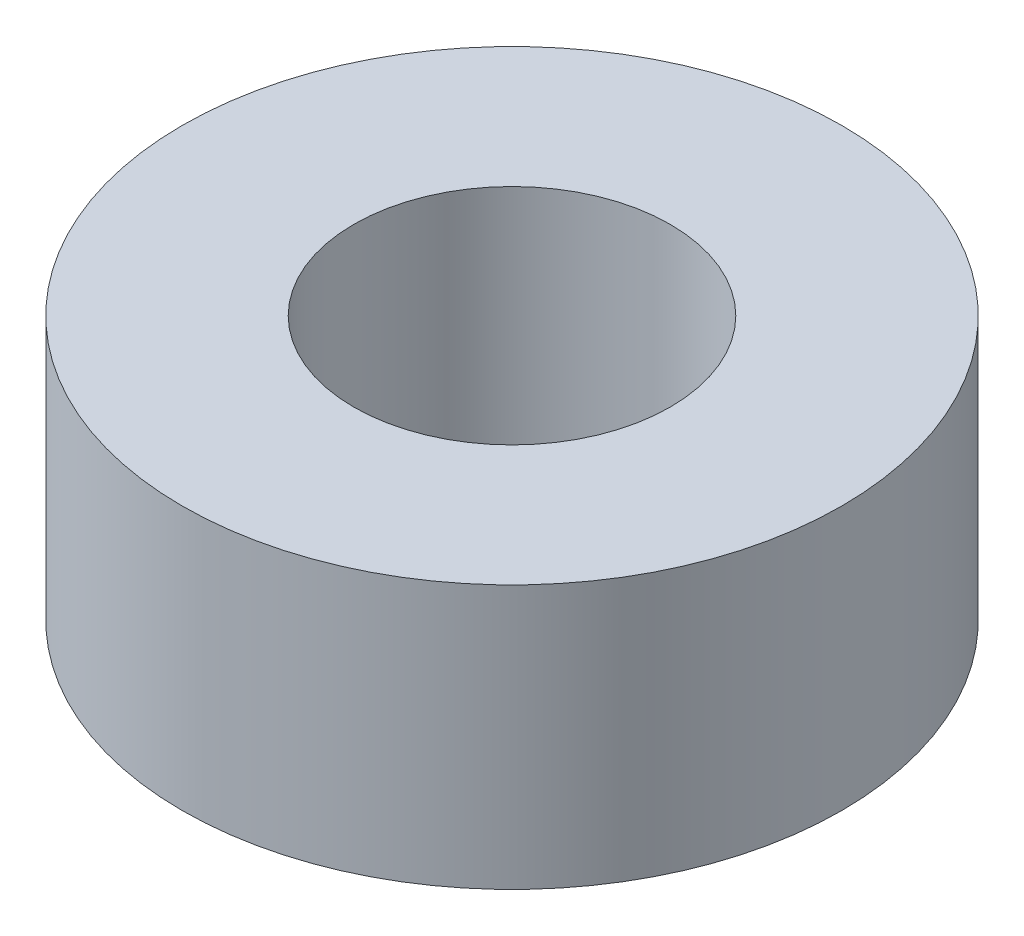
SolidWorks part; units mm, degrees
material "Aluminum Bronze"
ref_plane "Front Plane" through (0, 0, 0) normal (0, 0, 1) x (1, 0, 0)
ref_plane "Top Plane" through (0, 0, 0) normal (0, 1, 0) x (1, 0, 0)
ref_plane "Right Plane" through (0, 0, 0) normal (1, 0, 0) x (0, 0, -1)
sketch "Sketch1" plane through (0, 0, 0) normal (0, 1, 0) x (1, 0, 0)
  circle A0 centre (0, 0) radius 2.4
  circle A1 centre (0, 0) radius 5
extrude "Boss-Extrude1" add sketch "Sketch1" along normal blind 4
